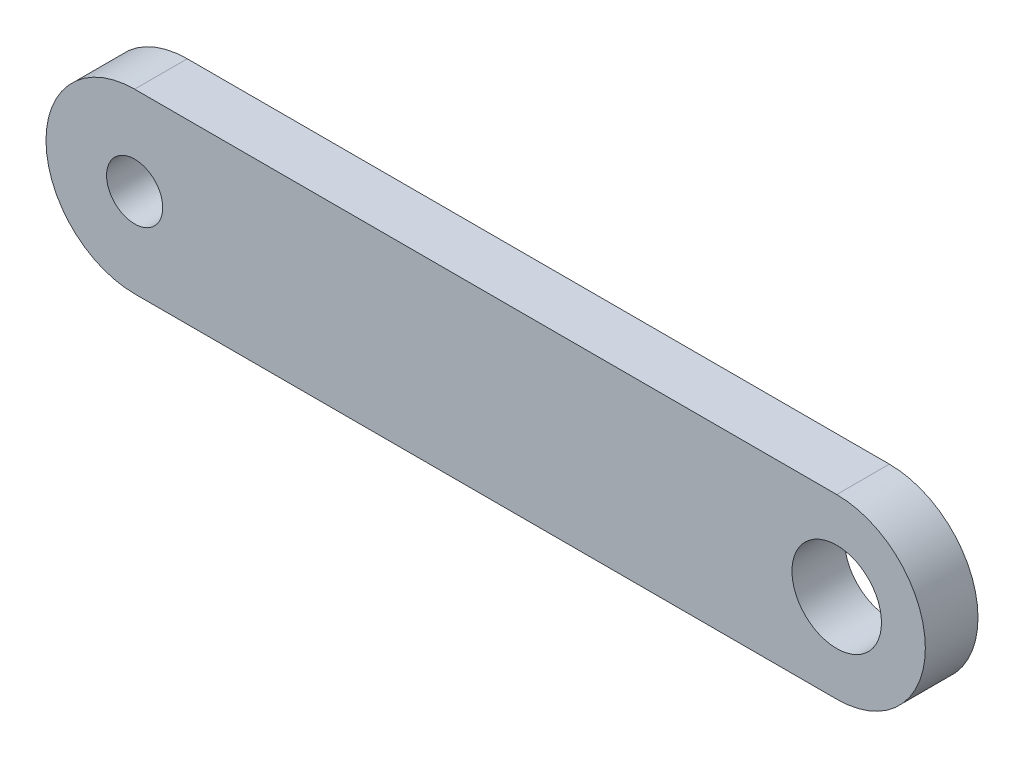
SolidWorks part; units mm, degrees
material "Thornel Mat VMA"
ref_plane "前视基准面" through (0, 0, 0) normal (0, 0, 1) x (1, 0, 0)
ref_plane "上视基准面" through (0, 0, 0) normal (0, 1, 0) x (1, 0, 0)
ref_plane "右视基准面" through (0, 0, 0) normal (1, 0, 0) x (0, 0, -1)
sketch "草图1" plane through (0, 0, 0) normal (0, 0, 1) x (1, 0, 0)
  line L0 (-20, 0) -> (20, 0) construction
  line L1 (-20, 0) -> (20, 0) construction
  line L2 (-20, 5.05) -> (20, 5.05)
  line L3 (-20, -5.05) -> (20, -5.05)
  circle A0 centre (-20, 0) radius 1.6
  circle A1 centre (20, 0) radius 2.55
  arc A2 (-20, 5.05) -> (-20, -5.05) centre (-20, 0) ccw
  arc A3 (20, -5.05) -> (20, 5.05) centre (20, 0) ccw
  point P5 (0, 0)
  dimension "D2" = 3.2
  dimension "D3" = 5.1
  dimension "D4" = 2.5
  dimension "D1" = 40
extrude "凸台-拉伸1" add sketch "草图1" along normal blind 3
